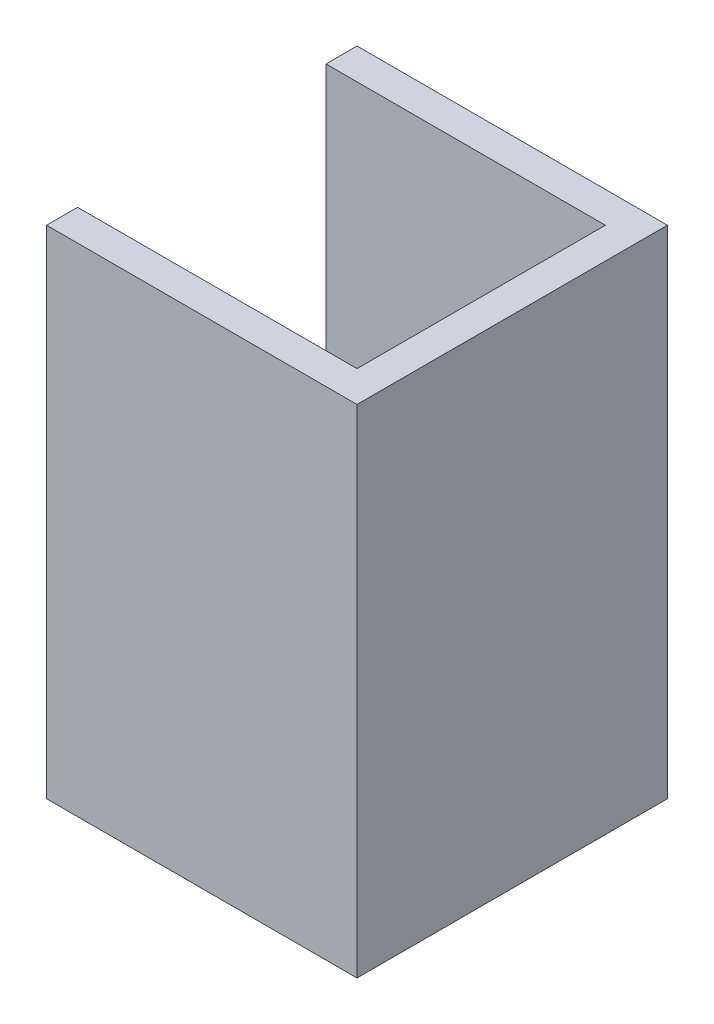
SolidWorks part; units mm, degrees
ref_plane "Front Plane" through (0, 0, 0) normal (0, 0, 1) x (1, 0, 0)
ref_plane "Top Plane" through (0, 0, 0) normal (0, 1, 0) x (1, 0, 0)
ref_plane "Right Plane" through (0, 0, 0) normal (1, 0, 0) x (0, 0, -1)
sketch "Sketch1" plane through (0, 0, 0) normal (0, 1, 0) x (1, 0, 0)
  line L0 (-12.5, 10) -> (-12.5, 12.5)
  line L1 (12.5, -12.5) -> (-12.5, -12.5)
  line L2 (12.5, -12.5) -> (12.5, 12.5)
  line L3 (12.5, 12.5) -> (-12.5, 12.5)
  line L4 (-12.5, -12.5) -> (-12.5, -10)
  line L5 (12.5, -12.5) -> (-12.5, 12.5) construction
  line L6 (12.5, 12.5) -> (-12.5, -12.5) construction
  line L7 (10, -10) -> (-12.5, -10)
  line L8 (10, -10) -> (10, 10)
  line L9 (10, 10) -> (-12.5, 10)
  line L11 (-1.25, 10) -> (-1.25, -10) construction
  line L12 (10, 0) -> (-10, 0) construction
  point P0 (0, 0)
  point P70 (-1.25, 0)
  dimension "D1" = 25
  dimension "D2" = 22.5
  dimension "D3" = 20
extrude "Boss-Extrude1" add sketch "Sketch1" along normal blind 40
equation "\"D2@Sketch1\"=\"D1@Sketch1\"-2.5"
equation "\"D3@Sketch1\"=\"D1@Sketch1\"-5"
